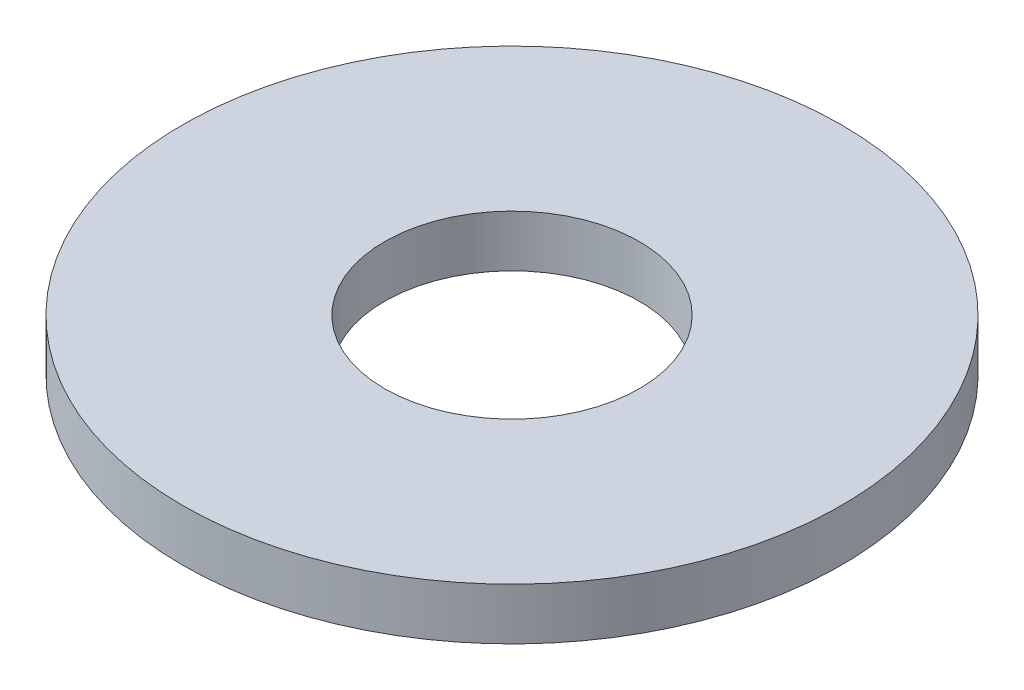
SolidWorks part; units mm, degrees
ref_plane "Front Plane" through (0, 0, 0) normal (0, 0, 1) x (1, 0, 0)
ref_plane "Top Plane" through (0, 0, 0) normal (0, 1, 0) x (1, 0, 0)
ref_plane "Right Plane" through (0, 0, 0) normal (1, 0, 0) x (0, 0, -1)
sketch "Sketch1" plane through (0, 0, 0) normal (0, 1, 0) x (1, 0, 0)
  circle A0 centre (0, 0) radius 8.7376
  dimension "OD" = 17.4752
extrude "Boss-Extrude1" add sketch "Sketch1" along normal blind 1.3716
sketch "Sketch5" plane through (0, 1.3716, 0) normal (0, 1, 0) x (-1, 0, 0)
  circle A0 centre (0, 0) radius 3.3782
  dimension "ID" = 6.7564
extrude "Cut-Extrude1" cut sketch "Sketch5" against normal through all
